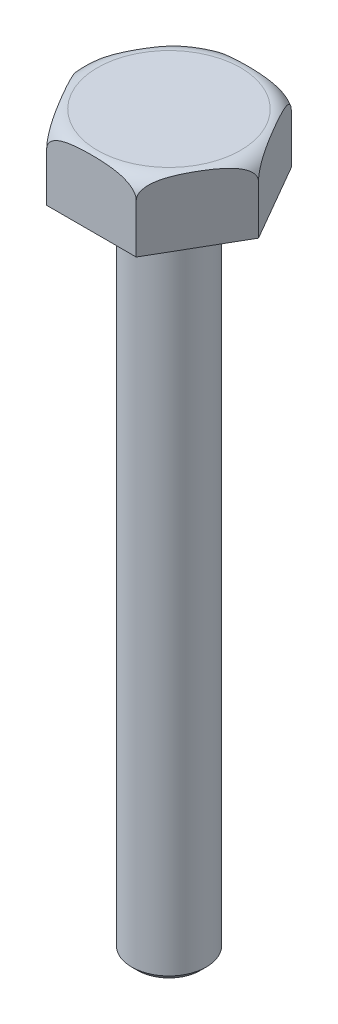
SolidWorks part; units mm, degrees
ref_plane "Front Plane" through (0, 0, 0) normal (0, 0, 1) x (1, 0, 0)
ref_plane "Top Plane" through (0, 0, 0) normal (0, 1, 0) x (1, 0, 0)
ref_plane "Right Plane" through (0, 0, 0) normal (1, 0, 0) x (0, 0, -1)
sketch "Sketch3" plane through (0, 0, 0) normal (0, 1, 0) x (1, 0, 0)
  circle A0 centre (0, 0) radius 25
  dimension "D1" = 50
extrude "Boss-Extrude2" add sketch "Sketch3" along normal blind 445
sketch "Sketch4" plane through (0, 445, 0) normal (0, 1, 0) x (1, 0, 0)
  line L1 (60.0444, 0) -> (30.0222, 52)
  line L2 (30.0222, 52) -> (-30.0222, 52)
  line L3 (-30.0222, 52) -> (-60.0444, 0)
  line L4 (-60.0444, 0) -> (-30.0222, -52)
  line L5 (-30.0222, -52) -> (30.0222, -52)
  line L6 (30.0222, -52) -> (60.0444, 0)
  circle A0 centre (0, 0) radius 52 construction
  dimension "D1" = 104
extrude "Boss-Extrude3" add sketch "Sketch4" along normal blind 45
chamfer "Chamfer2" distance 4 angle 45 1 edges at (0, 0, 25)
sketch "Sketch5" plane through (0, 0, 0) normal (0, 0, 1) x (1, 0, 0)
  line L0 (-48.0444, 490) -> (-42.4228, 490)
  line L1 (-60.0444, 490) -> (-30.0222, 490) construction
  line L2 (-42.4228, 490) -> (-58.618, 506.1952)
  line L3 (-58.618, 506.1952) -> (-76.9098, 483.5431)
  line L4 (-76.9098, 483.5431) -> (-60.0444, 474.0294)
  line L5 (-60.0444, 490) -> (-60.0444, 445) construction
  line L6 (-60.0444, 474.0294) -> (-60.0444, 478)
  line L7 (0, 490.8104) -> (0, 511.0269) construction
  arc A0 (-48.0444, 490) -> (-60.0444, 478) centre (-48.0444, 478) ccw
  point P12 (-60.0444, 490)
  dimension "D1" = 12
revolve "Cut-Revolve1" cut sketch "Sketch5" angle 360 about L7
